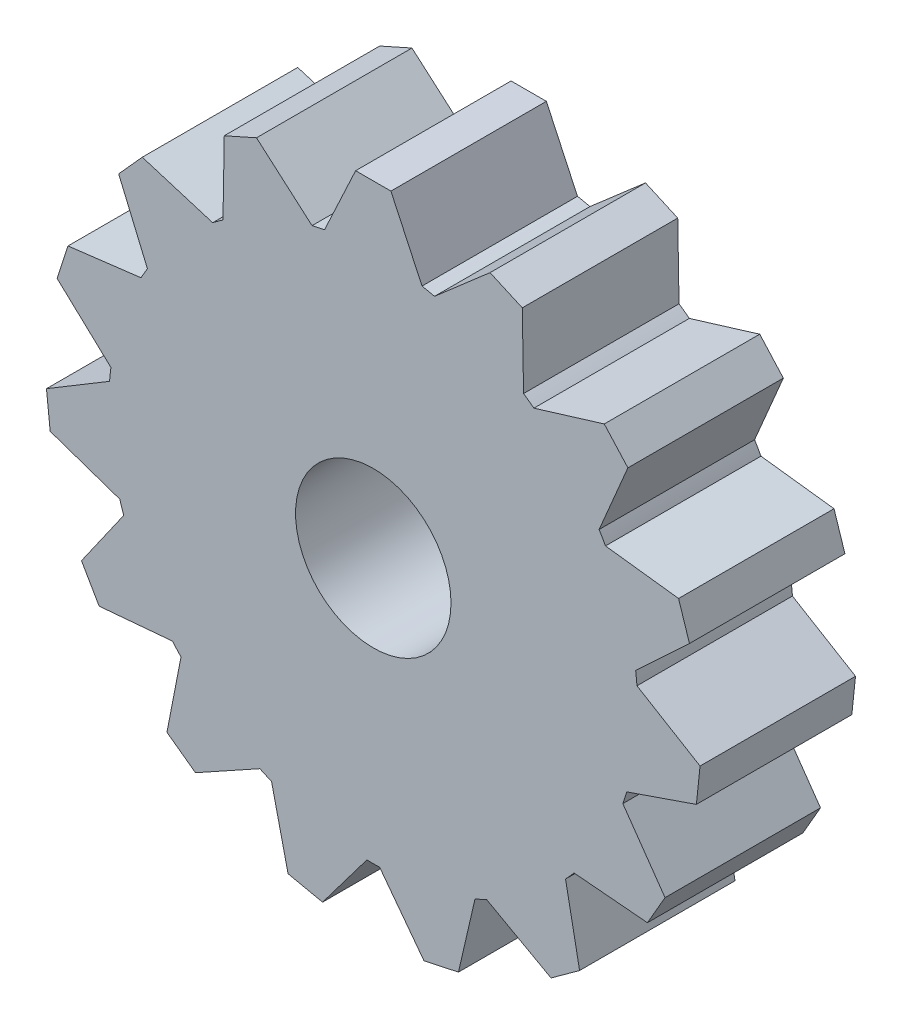
SolidWorks part; units mm, degrees
ref_plane "Front Plane" through (0, 0, 0) normal (0, 0, 1) x (1, 0, 0)
ref_plane "Top Plane" through (0, 0, 0) normal (0, 1, 0) x (1, 0, 0)
ref_plane "Right Plane" through (0, 0, 0) normal (1, 0, 0) x (0, 0, -1)
sketch "Sketch1" plane through (0, 0, 0) normal (0, 0, 1) x (1, 0, 0)
  line L0 (4.8312, 7.1631) -> (4.7926, 9.3695)
  line L1 (3.756, 9.831) -> (4.7926, 9.3695)
  line L2 (-1.5, 8.5088) -> (-0.5674, 10.5088)
  line L3 (2.0905, 8.3833) -> (3.756, 9.831)
  line L4 (2.1834, 8.464) -> (1.9692, 8.2778)
  line L5 (1.5, 8.5088) -> (0.5674, 10.5088)
  line L6 (-1.448, 8.6204) -> (-1.5679, 8.3631)
  line L7 (-0.5674, 10.5088) -> (0.5674, 10.5088)
  line L8 (1.448, 8.6204) -> (1.5679, 8.3631)
  line L9 (4.829, 7.2861) -> (4.834, 7.0023)
  line L10 (7.327, 4.5788) -> (8.1892, 6.6101)
  line L11 (7.4299, 7.4534) -> (8.1892, 6.6101)
  line L12 (5.3196, 6.8082) -> (7.4299, 7.4534)
  line L13 (5.4373, 6.8442) -> (5.1658, 6.7612)
  line L14 (7.3751, 4.6921) -> (7.2641, 4.4308)
  line L15 (8.5559, 1.2028) -> (10.1698, 2.7078)
  line L16 (9.8191, 3.787) -> (10.1698, 2.7078)
  line L17 (7.6288, 4.0559) -> (9.8191, 3.787)
  line L18 (7.751, 4.0409) -> (7.4692, 4.0755)
  line L19 (8.6459, 1.2867) -> (8.4383, 1.0931)
  line L20 (8.3054, -2.3812) -> (10.3919, -1.6627)
  line L21 (10.5105, -0.5342) -> (10.3919, -1.6627)
  line L22 (8.619, 0.6024) -> (10.5105, -0.5342)
  line L23 (8.7245, 0.539) -> (8.4812, 0.6852)
  line L24 (8.4218, -2.3411) -> (8.1534, -2.4335)
  line L25 (6.6188, -5.5534) -> (8.8172, -5.7458)
  line L26 (9.3846, -4.763) -> (8.8172, -5.7458)
  line L27 (8.1188, -2.9554) -> (9.3846, -4.763)
  line L28 (8.1894, -3.0562) -> (8.0266, -2.8237)
  line L29 (6.7415, -5.5642) -> (6.4587, -5.5394)
  line L30 (3.7878, -7.7654) -> (5.7179, -8.8353)
  line L31 (6.6359, -8.1683) -> (5.7179, -8.8353)
  line L32 (6.2149, -6.0021) -> (6.6359, -8.1683)
  line L33 (6.2384, -6.1229) -> (6.1842, -5.8443)
  line L34 (3.8955, -7.8251) -> (3.6472, -7.6875)
  line L35 (0.3019, -8.6347) -> (1.6299, -10.3971)
  line L36 (2.7399, -10.1612) -> (1.6299, -10.3971)
  line L37 (3.2363, -8.011) -> (2.7399, -10.1612)
  line L38 (3.2086, -8.1309) -> (3.2725, -7.8543)
  line L39 (0.3759, -8.733) -> (0.2051, -8.5063)
  line L40 (-3.2363, -8.011) -> (-2.7399, -10.1612)
  line L41 (-1.6299, -10.3971) -> (-2.7399, -10.1612)
  line L42 (-0.3019, -8.6347) -> (-1.6299, -10.3971)
  line L43 (-0.3759, -8.733) -> (-0.2051, -8.5063)
  line L44 (-3.2086, -8.1309) -> (-3.2725, -7.8543)
  line L45 (-6.2149, -6.0021) -> (-6.6359, -8.1683)
  line L46 (-5.7179, -8.8353) -> (-6.6359, -8.1683)
  line L47 (-3.7878, -7.7654) -> (-5.7179, -8.8353)
  line L48 (-3.8955, -7.8251) -> (-3.6472, -7.6875)
  line L49 (-6.2384, -6.1229) -> (-6.1842, -5.8443)
  line L50 (-8.1188, -2.9554) -> (-9.3846, -4.763)
  line L51 (-8.8172, -5.7458) -> (-9.3846, -4.763)
  line L52 (-6.6188, -5.5534) -> (-8.8172, -5.7458)
  line L53 (-6.7415, -5.5642) -> (-6.4587, -5.5394)
  line L54 (-8.1894, -3.0562) -> (-8.0266, -2.8237)
  line L55 (-8.619, 0.6024) -> (-10.5105, -0.5342)
  line L56 (-10.3919, -1.6627) -> (-10.5105, -0.5342)
  line L57 (-8.3054, -2.3812) -> (-10.3919, -1.6627)
  line L58 (-8.4218, -2.3411) -> (-8.1534, -2.4335)
  line L59 (-8.7245, 0.539) -> (-8.4812, 0.6852)
  line L60 (-7.6288, 4.0559) -> (-9.8191, 3.787)
  line L61 (-10.1698, 2.7078) -> (-9.8191, 3.787)
  line L62 (-8.5559, 1.2028) -> (-10.1698, 2.7078)
  line L63 (-8.6459, 1.2867) -> (-8.4383, 1.0931)
  line L64 (-7.751, 4.0409) -> (-7.4692, 4.0755)
  line L65 (-5.3196, 6.8082) -> (-7.4299, 7.4534)
  line L66 (-8.1892, 6.6101) -> (-7.4299, 7.4534)
  line L67 (-7.327, 4.5788) -> (-8.1892, 6.6101)
  line L68 (-7.3751, 4.6921) -> (-7.2641, 4.4308)
  line L69 (-5.4373, 6.8442) -> (-5.1658, 6.7612)
  line L70 (-2.0905, 8.3833) -> (-3.756, 9.831)
  line L71 (-4.7926, 9.3695) -> (-3.756, 9.831)
  line L72 (-4.8312, 7.1631) -> (-4.7926, 9.3695)
  line L73 (-4.829, 7.2861) -> (-4.834, 7.0023)
  line L74 (-2.1834, 8.464) -> (-1.9692, 8.2778)
  arc A0 (-1.5679, 8.3631) -> (-1.9692, 8.2778) centre (0, 0) ccw
  arc A1 (-4.834, 7.0023) -> (-5.1658, 6.7612) centre (0, 0) ccw
  arc A2 (1.9692, 8.2778) -> (1.5679, 8.3631) centre (0, 0) ccw
  arc A3 (5.1658, 6.7612) -> (4.834, 7.0023) centre (0, 0) ccw
  arc A4 (7.4692, 4.0755) -> (7.2641, 4.4308) centre (0, 0) ccw
  arc A5 (8.4812, 0.6852) -> (8.4383, 1.0931) centre (0, 0) ccw
  arc A6 (8.0266, -2.8237) -> (8.1534, -2.4335) centre (0, 0) ccw
  arc A7 (6.1842, -5.8443) -> (6.4587, -5.5394) centre (0, 0) ccw
  arc A8 (3.2725, -7.8543) -> (3.6472, -7.6875) centre (0, 0) ccw
  arc A9 (-0.2051, -8.5063) -> (0.2051, -8.5063) centre (0, 0) ccw
  arc A10 (-3.6472, -7.6875) -> (-3.2725, -7.8543) centre (0, 0) ccw
  arc A11 (-6.4587, -5.5394) -> (-6.1842, -5.8443) centre (0, 0) ccw
  arc A12 (-8.1534, -2.4335) -> (-8.0266, -2.8237) centre (0, 0) ccw
  arc A13 (-8.4383, 1.0931) -> (-8.4812, 0.6852) centre (0, 0) ccw
  arc A14 (-7.2641, 4.4308) -> (-7.4692, 4.0755) centre (0, 0) ccw
  circle A15 centre (0, 0) radius 2.5
  point P125 (0, 0)
  dimension "D1" = 15
  dimension "D4" = 2
extrude "Boss-Extrude1" add sketch "Sketch1" along normal blind 5 contours L68 A14 L64 L60 L61 L62 L63 A13 L59 L55 L56 L57 L58 A12 L54 L50 L51 L52 L53 A11 L49 L45 L46 L47 L48 A10 L44 L40 L41 L42 L43 A9 L39 L35 L36 L37 L38 A8 L34
